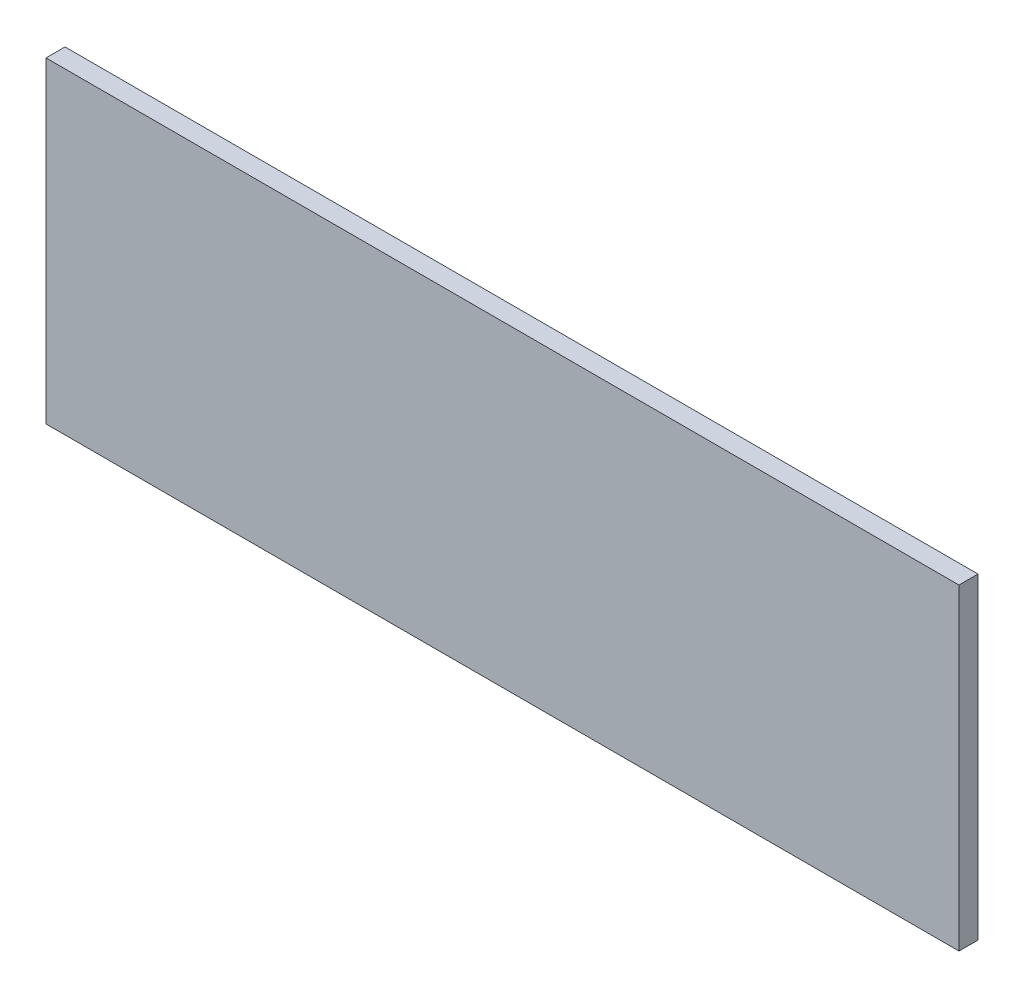
SolidWorks part; units mm, degrees
ref_plane "Front Plane" through (0, 0, 0) normal (0, 0, 1) x (1, 0, 0)
ref_plane "Top Plane" through (0, 0, 0) normal (0, 1, 0) x (1, 0, 0)
ref_plane "Right Plane" through (0, 0, 0) normal (1, 0, 0) x (0, 0, -1)
sketch "Sketch1" plane through (0, 0, 0) normal (0, 0, 1) x (1, 0, 0)
  line L0 (-72, 25) -> (-75, 25) construction
  line L1 (-72, 25) -> (72, 25)
  line L2 (-72, 25) -> (-72, -25)
  line L3 (-72, -25) -> (72, -25)
  line L4 (72, 25) -> (72, -25)
  point P4 (0, -25)
  point P6 (72, 0)
  point P7 (0, 0)
  point P9 (-72, -25)
  point P14 (0, 0)
extrude "Boss-Extrude1" add sketch "Sketch1" along normal blind 3
